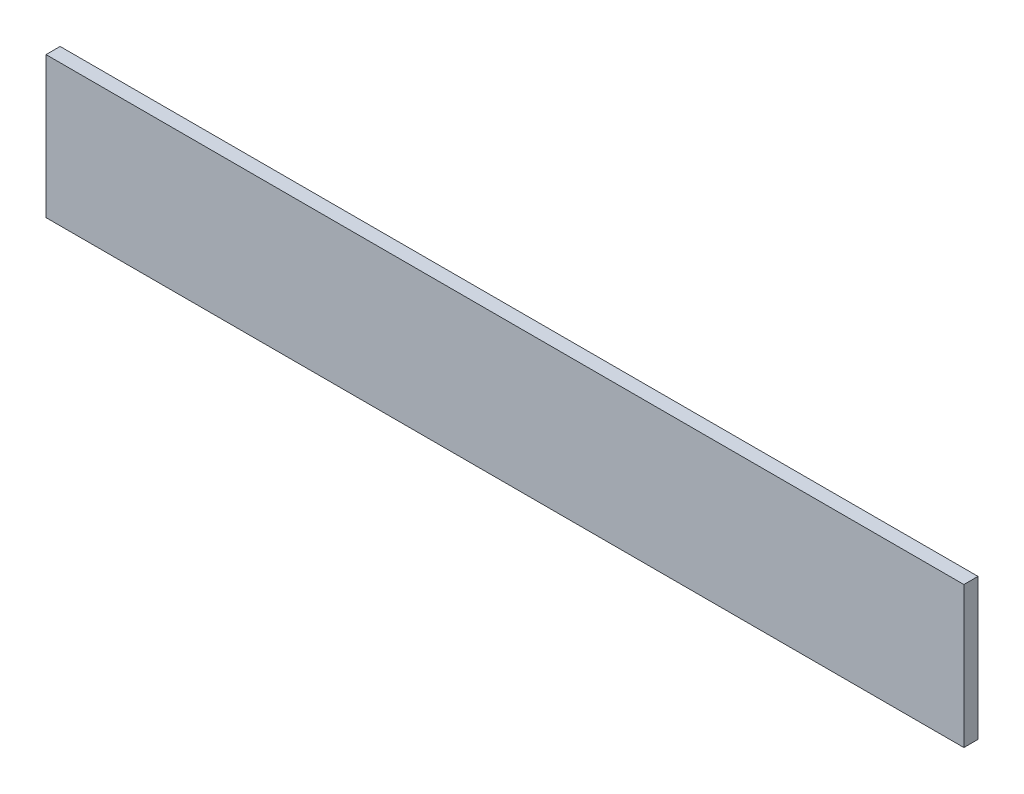
SolidWorks part; units mm, degrees
ref_plane "Спереди" through (0, 0, 0) normal (0, 0, 1) x (1, 0, 0)
ref_plane "Сверху" through (0, 0, 0) normal (0, 1, 0) x (1, 0, 0)
ref_plane "Справа" through (0, 0, 0) normal (1, 0, 0) x (0, 0, -1)
sketch "Эскиз1" plane through (0, 0, 0) normal (0, 0, 1) x (1, 0, 0)
  line L1 (0, 0) -> (130, 0)
  line L2 (0, 0) -> (0, -20)
  line L3 (0, -20) -> (130, -20)
  line L4 (130, 0) -> (130, -20)
extrude "Бобышка-Вытянуть1" add sketch "Эскиз1" along normal blind 2
